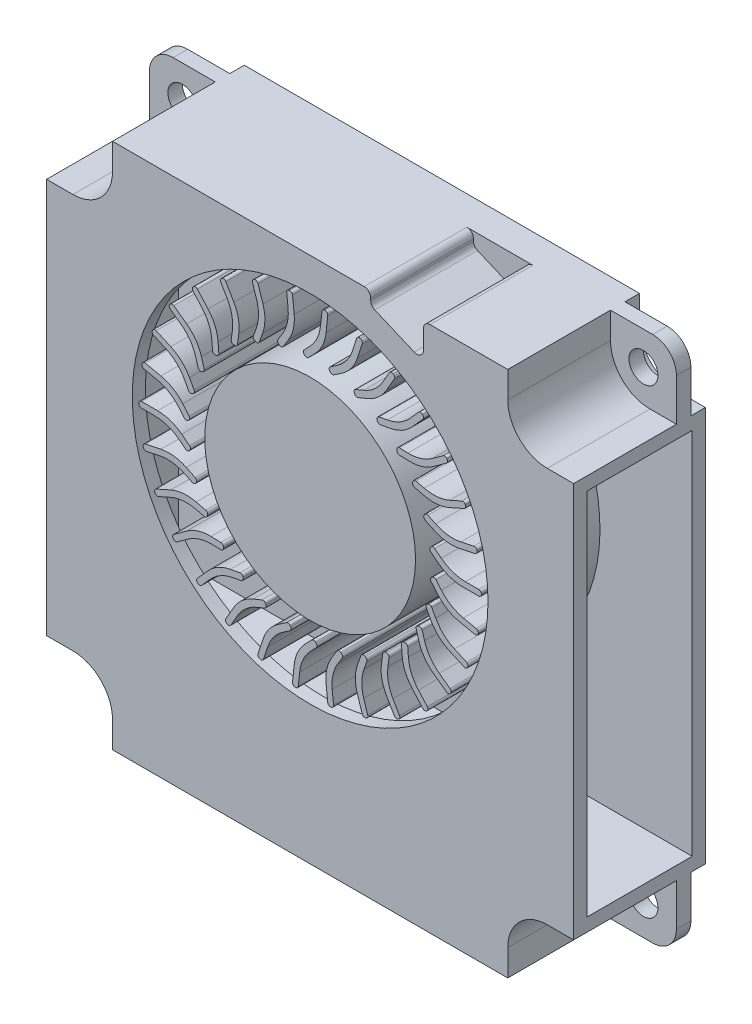
SolidWorks part; units mm, degrees
ref_plane "前视基准面" through (0, 0, 0) normal (0, 0, 1) x (1, 0, 0)
ref_plane "上视基准面" through (0, 0, 0) normal (0, 1, 0) x (1, 0, 0)
ref_plane "右视基准面" through (0, 0, 0) normal (1, 0, 0) x (0, 0, -1)
sketch "草图1" plane through (0, 0, 0) normal (0, 0, 1) x (1, 0, 0)
  line L0 (0, 0) -> (19303.9639, 0) construction
  line L1 (0, 0) -> (0, 19303.9639) construction
  line L3 (-18.2, 20) -> (18.2, 20)
  line L4 (-20, 18.2) -> (-20, -18.2)
  line L5 (-18.2, -20) -> (18.2, -20)
  line L6 (20, 18.2) -> (20, -18.2)
  circle A0 centre (17.5, 17.5) radius 1.1
  circle A1 centre (17.5, -17.5) radius 1.1
  circle A2 centre (-17.5, -17.5) radius 1.1
  circle A3 centre (-17.5, 17.5) radius 1.1
  arc A4 (-20, -18.2) -> (-18.2, -20) centre (-18.2, -18.2) ccw
  arc A5 (18.2, -20) -> (20, -18.2) centre (18.2, -18.2) ccw
  arc A6 (18.2, 20) -> (20, 18.2) centre (18.2, 18.2) cw
  arc A7 (-18.2, 20) -> (-20, 18.2) centre (-18.2, 18.2) ccw
  point P20 (0, 0)
  point P22 (20, -20)
  point P25 (20, 20)
  point P28 (-20, 20)
  point P29 (0, 0)
  point P30 (0, 0)
  point P31 (0, 0)
  point P32 (0, 0)
  point P33 (0, 0)
  point P34 (0, 0)
  point P35 (0, 0)
  point P36 (0, 0)
  point P37 (0, 0)
  point P38 (13.6155, 15.9544)
  point P39 (14.9053, -16.2042)
  point P40 (0, 0)
  point P41 (0, 0)
  point P42 (-13.1755, -15.2334)
  point P43 (-10.9074, 13.5723)
  point P44 (0, 0)
  point P45 (0, 0)
  point P46 (0, 0)
  point P47 (0, 0)
  point P48 (0, 0)
  point P49 (0, 0)
  dimension "D3" = 2.2
  dimension "D4" = 35
  dimension "D5" = 35
  dimension "D7" = 1.8
  dimension "D1" = 40
  dimension "D2" = 40
extrude "凸台-拉伸1" add sketch "草图1" along normal blind 1.1
sketch "草图2" plane through (0, 0, 1.1) normal (0, 0, 1) x (1, 0, 0)
  line L0 (0, 0) -> (50000, 0) construction
  line L1 (0, 0) -> (0, 50000) construction
  line L2 (-20, 15) -> (-18, 15)
  line L3 (-15, 20) -> (4.1, 20)
  line L4 (-20, 15) -> (-20, -15)
  line L5 (-15, -20) -> (15, -20)
  line L6 (20, 15) -> (20, -15)
  line L7 (-15, 18) -> (-15, 20)
  line L8 (18, 15) -> (20, 15)
  line L9 (15, 20) -> (15, 18)
  line L10 (15, -18) -> (15, -20)
  line L11 (20, -15) -> (18, -15)
  line L12 (-18, -15) -> (-20, -15)
  line L13 (-15, -20) -> (-15, -18)
  line L14 (8.6, 19.5) -> (8.6, 18.0558)
  line L15 (7.9044, 17.5956) -> (4.9044, 18.8706)
  line L16 (4.6, 19.3308) -> (4.6, 19.5)
  line L17 (9.1, 20) -> (15, 20)
  arc A0 (-18, -15) -> (-15, -18) centre (-18, -18) cw
  arc A1 (15, -18) -> (18, -15) centre (18, -18) cw
  arc A2 (18, 15) -> (15, 18) centre (18, 18) cw
  arc A3 (-18, 15) -> (-15, 18) centre (-18, 18) ccw
  arc A4 (4.9044, 18.8706) -> (4.6, 19.3308) centre (5.1, 19.3308) cw
  arc A5 (4.6, 19.5) -> (4.1, 20) centre (4.1, 19.5) ccw
  arc A6 (8.6, 19.5) -> (9.1, 20) centre (9.1, 19.5) cw
  arc A7 (8.6, 18.0558) -> (7.9044, 17.5956) centre (8.1, 18.0558) cw
  point P24 (0, 0)
  point P26 (-15, 15)
  point P33 (4.6, 19)
  point P36 (4.6, 20)
  point P39 (8.6, 20)
  point P42 (8.6, 17.3)
  dimension "D1" = 3
  dimension "D13" = 0.5
  dimension "D2" = 40
  dimension "D3" = 5
  dimension "D4" = 5
  dimension "D6" = 40
  dimension "D7" = 5
  dimension "D8" = 5
  dimension "D9" = 6.4
  dimension "D10" = 2.7
  dimension "D11" = 4
  dimension "D12" = 1
  dimension "D5" = 4
extrude "凸台-拉伸2" add sketch "草图2" along normal blind 7.8
sketch "草图3" plane through (0, 0, 0) normal (0, 0, -1) x (-1, 0, 0)
  line L0 (0, 0) -> (50000, 0) construction
  line L1 (-15, 20) -> (15, 20)
  line L2 (-20, 15) -> (-20, -15)
  line L3 (-15, -20) -> (15, -20)
  line L4 (20, 15) -> (20, -15)
  line L5 (0, 0) -> (0, 50000) construction
  line L6 (-20, 15) -> (-18, 15)
  line L7 (-15, 18) -> (-15, 20)
  line L8 (18, 15) -> (20, 15)
  line L9 (15, 20) -> (15, 18)
  line L10 (15, -18) -> (15, -20)
  line L11 (20, -15) -> (18, -15)
  line L12 (-18, -15) -> (-20, -15)
  line L13 (-15, -20) -> (-15, -18)
  line L14 (-18.2, 20) -> (18.2, 20) construction
  arc A0 (-18, -15) -> (-15, -18) centre (-18, -18) cw
  arc A1 (15, -18) -> (18, -15) centre (18, -18) cw
  arc A2 (18, 15) -> (15, 18) centre (18, 18) cw
  arc A3 (-18, 15) -> (-15, 18) centre (-18, 18) ccw
  point P24 (0, 0)
  point P26 (-15, 15)
  dimension "D1" = 3
  dimension "D2" = 40
  dimension "D3" = 5
  dimension "D4" = 5
  dimension "D6" = 40
  dimension "D7" = 5
  dimension "D8" = 5
  dimension "D5" = 4
extrude "凸台-拉伸3" add sketch "草图3" along normal blind 1.1
sketch "草图4" plane through (20, 0, 0) normal (1, 0, 0) x (0, 0, -1)
  line L0 (1.1, 15) -> (1.1, -15) construction
  line L1 (-7.9, 14) -> (0.1, 14)
  line L2 (-7.9, 14) -> (-7.9, -14)
  line L3 (-7.9, -14) -> (0.1, -14)
  line L4 (0.1, 14) -> (0.1, -14)
  line L5 (-8.9, -15) -> (-8.9, 15) construction
  line L6 (-8.9, 15) -> (-1.1, 15) construction
  line L7 (-8.9, -15) -> (-1.1, -15) construction
  point P8 (-5, 15)
  dimension "D1" = 1
  dimension "D2" = 1
  dimension "D3" = 1
  dimension "D4" = 1
extrude "切除-拉伸1" cut sketch "草图4" against normal blind 39
sketch "草图5" plane through (0, 0, 8.9) normal (0, 0, 1) x (1, 0, 0)
  line L0 (4.1, 20) -> (-15, 20) construction
  circle A0 centre (0, 4) radius 13.5
  dimension "D2" = 27
  dimension "D1" = 16
extrude "切除-拉伸2" cut sketch "草图5" against normal blind 9
sketch "草图6" plane through (0, 0, -0.1) normal (0, 0, 1) x (1, 0, 0)
  circle A0 centre (0, 4) radius 13
  dimension "D1" = 26
extrude "凸台-拉伸4" add sketch "草图6" along normal blind 1
sketch "草图7" plane through (0, 0, 0.9) normal (0, 0, 1) x (1, 0, 0)
  line L0 (0, 4) -> (50000, 4) construction
  line L1 (0.3943, 4.0838) -> (48907.7743, 10399.6683) construction
  line L2 (12.7966, 4) -> (11.5807, 4)
  line L3 (9.7456, 4.6267) -> (9.1582, 5.0809)
  line L4 (9.1223, 5.3615) -> (9.1713, 5.4248)
  line L5 (9.4519, 5.4607) -> (9.9575, 5.0697)
  line L6 (11.7926, 4.443) -> (12.7958, 4.443)
  line L7 (12.9958, 4.2464) -> (12.9965, 4.2034)
  line L8 (12.5169, 1.3394) -> (11.3276, 1.5922)
  line L9 (9.6629, 2.5868) -> (9.1828, 3.1532)
  line L10 (9.2061, 3.4351) -> (9.2671, 3.4869)
  line L11 (9.549, 3.4636) -> (9.9623, 2.9761)
  line L12 (11.627, 1.9815) -> (12.6083, 1.7729)
  line L13 (12.763, 1.539) -> (12.7548, 1.4968)
  line L14 (11.6902, -1.2048) -> (10.5795, -0.7103)
  line L15 (9.158, 0.6087) -> (8.8061, 1.2625)
  line L16 (8.8874, 1.5334) -> (8.9579, 1.5713)
  line L17 (9.2288, 1.49) -> (9.5317, 0.9272)
  line L18 (10.9532, -0.3918) -> (11.8698, -0.7998)
  line L19 (11.9725, -1.0608) -> (11.9557, -1.1003)
  line L20 (10.3526, -3.5216) -> (9.369, -2.807)
  line L21 (8.2527, -1.2213) -> (8.0445, -0.5086)
  line L22 (8.1804, -0.2605) -> (8.2572, -0.2381)
  line L23 (8.5053, -0.3739) -> (8.6845, -0.9874)
  line L24 (9.8008, -2.5731) -> (10.6124, -3.1628)
  line L25 (10.6587, -3.4394) -> (10.634, -3.4746)
  line L26 (8.5626, -5.5097) -> (7.749, -4.6061)
  line L27 (6.9868, -2.823) -> (6.9313, -2.0826)
  line L28 (7.1158, -1.8682) -> (7.1956, -1.8622)
  line L29 (7.41, -2.0467) -> (7.4578, -2.684)
  line L30 (8.22, -4.4672) -> (8.8913, -5.2127)
  line L31 (8.879, -5.4929) -> (8.8475, -5.5222)
  line L32 (6.3983, -7.0821) -> (5.7904, -6.0292)
  line L33 (5.4156, -4.1266) -> (5.5152, -3.3908)
  line L34 (5.7403, -3.2194) -> (5.8196, -3.2302)
  line L35 (5.9909, -3.4552) -> (5.9052, -4.0885)
  line L36 (6.2799, -5.9912) -> (6.7816, -6.86)
  line L37 (6.7113, -7.1315) -> (6.6744, -7.1536)
  line L38 (3.9544, -8.1703) -> (3.5786, -7.0139)
  line L39 (3.6076, -5.0749) -> (3.8581, -4.376)
  line L40 (4.1138, -4.2551) -> (4.1892, -4.2821)
  line L41 (4.31, -4.5379) -> (4.0944, -5.1395)
  line L42 (4.0654, -7.0785) -> (4.3754, -8.0327)
  line L43 (4.2503, -8.2836) -> (4.2096, -8.2976)
  line L44 (1.3376, -8.7265) -> (1.2105, -7.5173)
  line L45 (1.642, -5.6267) -> (2.0323, -4.9951)
  line L46 (2.3076, -4.9301) -> (2.3757, -4.9721)
  line L47 (2.4407, -5.2474) -> (2.1047, -5.7911)
  line L48 (1.6732, -7.6817) -> (1.7781, -8.6794)
  line L49 (1.6035, -8.8989) -> (1.5608, -8.9041)
  line L50 (-1.3376, -8.7265) -> (-1.2105, -7.5173)
  line L51 (-0.3954, -5.7577) -> (0.1177, -5.221)
  line L52 (0.4005, -5.2147) -> (0.4583, -5.27)
  line L53 (0.4647, -5.5528) -> (0.023, -6.0147)
  line L54 (-0.7921, -7.7743) -> (-0.897, -8.772)
  line L55 (-1.1134, -8.9504) -> (-1.1562, -8.9466)
  line L56 (-3.9544, -8.1703) -> (-3.5786, -7.0139)
  line L57 (-2.4155, -5.4623) -> (-1.802, -5.044)
  line L58 (-1.5241, -5.0966) -> (-1.479, -5.1627)
  line L59 (-1.5316, -5.4406) -> (-2.0596, -5.8007)
  line L60 (-3.2228, -7.3523) -> (-3.5328, -8.3065)
  line L61 (-3.7816, -8.4359) -> (-3.8227, -8.4233)
  line L62 (-6.3983, -7.0821) -> (-5.7904, -6.0292)
  line L63 (-4.33, -4.7533) -> (-3.643, -4.4717)
  line L64 (-3.3821, -4.5809) -> (-3.3517, -4.655)
  line L65 (-3.4609, -4.9159) -> (-4.0523, -5.1583)
  line L66 (-5.5126, -6.4342) -> (-6.0143, -7.303)
  line L67 (-6.2845, -7.3779) -> (-6.3221, -7.357)
  line L68 (-8.5626, -5.5097) -> (-7.749, -4.6061)
  line L69 (-6.0553, -3.6618) -> (-5.3248, -3.5292)
  line L70 (-5.0923, -3.6902) -> (-5.078, -3.769)
  line L71 (-5.239, -4.0015) -> (-5.8679, -4.1156)
  line L72 (-7.5616, -5.06) -> (-8.2329, -5.8056)
  line L73 (-8.5128, -5.8226) -> (-8.5452, -5.7944)
  line L74 (-10.3526, -3.5216) -> (-9.369, -2.807)
  line L75 (-7.516, -2.2354) -> (-6.7738, -2.2576)
  line L76 (-6.5799, -2.4634) -> (-6.5823, -2.5435)
  line L77 (-6.7881, -2.7374) -> (-7.427, -2.7183)
  line L78 (-9.28, -3.2899) -> (-10.0917, -3.8796)
  line L79 (-10.369, -3.8381) -> (-10.3949, -3.8037)
  line L80 (-11.6902, -1.2048) -> (-10.5795, -0.7103)
  line L81 (-8.6481, -0.5365) -> (-7.9268, -0.7125)
  line L82 (-7.7799, -0.9542) -> (-7.7989, -1.0319)
  line L83 (-8.0406, -1.1788) -> (-8.6615, -1.0273)
  line L84 (-10.5929, -1.2012) -> (-11.5094, -1.6092)
  line L85 (-11.772, -1.511) -> (-11.7902, -1.472)
  line L86 (-12.5169, 1.3394) -> (-11.3276, 1.5922)
  line L87 (-9.4023, 1.3607) -> (-8.7333, 1.0386)
  line L88 (-8.6399, 0.7716) -> (-8.6747, 0.6995)
  line L89 (-8.9416, 0.6061) -> (-9.5175, 0.8834)
  line L90 (-11.4428, 1.1149) -> (-12.4241, 0.9063)
  line L91 (-12.6606, 1.057) -> (-12.6702, 1.0989)
  line L92 (-12.7966, 4) -> (-11.5807, 4)
  line L93 (-9.7456, 3.3733) -> (-9.1582, 2.9191)
  line L94 (-9.1223, 2.6385) -> (-9.1713, 2.5752)
  line L95 (-9.4519, 2.5393) -> (-9.9575, 2.9303)
  line L96 (-11.7926, 3.557) -> (-12.7958, 3.557)
  line L97 (-12.9958, 3.7536) -> (-12.9965, 3.7966)
  line L98 (-12.5169, 6.6606) -> (-11.3276, 6.4078)
  line L99 (-9.6629, 5.4132) -> (-9.1828, 4.8468)
  line L100 (-9.2061, 4.5649) -> (-9.2671, 4.5131)
  line L101 (-9.549, 4.5364) -> (-9.9623, 5.0239)
  line L102 (-11.627, 6.0185) -> (-12.6083, 6.2271)
  line L103 (-12.763, 6.461) -> (-12.7548, 6.5032)
  line L104 (-11.6902, 9.2048) -> (-10.5795, 8.7103)
  line L105 (-9.158, 7.3913) -> (-8.8061, 6.7375)
  line L106 (-8.8874, 6.4666) -> (-8.9579, 6.4287)
  line L107 (-9.2288, 6.51) -> (-9.5317, 7.0728)
  line L108 (-10.9532, 8.3918) -> (-11.8698, 8.7998)
  line L109 (-11.9725, 9.0608) -> (-11.9557, 9.1003)
  line L110 (-10.3526, 11.5216) -> (-9.369, 10.807)
  line L111 (-8.2527, 9.2213) -> (-8.0445, 8.5086)
  line L112 (-8.1804, 8.2605) -> (-8.2572, 8.2381)
  line L113 (-8.5053, 8.3739) -> (-8.6845, 8.9874)
  line L114 (-9.8008, 10.5731) -> (-10.6124, 11.1628)
  line L115 (-10.6587, 11.4394) -> (-10.634, 11.4746)
  line L116 (-8.5626, 13.5097) -> (-7.749, 12.6061)
  line L117 (-6.9868, 10.823) -> (-6.9313, 10.0826)
  line L118 (-7.1158, 9.8682) -> (-7.1956, 9.8622)
  line L119 (-7.41, 10.0467) -> (-7.4578, 10.684)
  line L120 (-8.22, 12.4672) -> (-8.8913, 13.2127)
  line L121 (-8.879, 13.4929) -> (-8.8475, 13.5222)
  line L122 (-6.3983, 15.0821) -> (-5.7904, 14.0292)
  line L123 (-5.4156, 12.1266) -> (-5.5152, 11.3908)
  line L124 (-5.7403, 11.2194) -> (-5.8196, 11.2302)
  line L125 (-5.9909, 11.4552) -> (-5.9052, 12.0885)
  line L126 (-6.2799, 13.9912) -> (-6.7816, 14.86)
  line L127 (-6.7113, 15.1315) -> (-6.6744, 15.1536)
  line L128 (-3.9544, 16.1703) -> (-3.5786, 15.0139)
  line L129 (-3.6076, 13.0749) -> (-3.8581, 12.376)
  line L130 (-4.1138, 12.2551) -> (-4.1892, 12.2821)
  line L131 (-4.31, 12.5379) -> (-4.0944, 13.1395)
  line L132 (-4.0654, 15.0785) -> (-4.3754, 16.0327)
  line L133 (-4.2503, 16.2836) -> (-4.2096, 16.2976)
  line L134 (-1.3376, 16.7265) -> (-1.2105, 15.5173)
  line L135 (-1.642, 13.6267) -> (-2.0323, 12.9951)
  line L136 (-2.3076, 12.9301) -> (-2.3757, 12.9721)
  line L137 (-2.4407, 13.2474) -> (-2.1047, 13.7911)
  line L138 (-1.6732, 15.6817) -> (-1.7781, 16.6794)
  line L139 (-1.6035, 16.8989) -> (-1.5608, 16.9041)
  line L140 (1.3376, 16.7265) -> (1.2105, 15.5173)
  line L141 (0.3954, 13.7577) -> (-0.1177, 13.221)
  line L142 (-0.4005, 13.2147) -> (-0.4583, 13.27)
  line L143 (-0.4647, 13.5528) -> (-0.023, 14.0147)
  line L144 (0.7921, 15.7743) -> (0.897, 16.772)
  line L145 (1.1134, 16.9504) -> (1.1562, 16.9466)
  line L146 (3.9544, 16.1703) -> (3.5786, 15.0139)
  line L147 (2.4155, 13.4623) -> (1.802, 13.044)
  line L148 (1.5241, 13.0966) -> (1.479, 13.1627)
  line L149 (1.5316, 13.4406) -> (2.0596, 13.8007)
  line L150 (3.2228, 15.3523) -> (3.5328, 16.3065)
  line L151 (3.7816, 16.4359) -> (3.8227, 16.4233)
  line L152 (6.3983, 15.0821) -> (5.7904, 14.0292)
  line L153 (4.33, 12.7533) -> (3.643, 12.4717)
  line L154 (3.3821, 12.5809) -> (3.3517, 12.655)
  line L155 (3.4609, 12.9159) -> (4.0523, 13.1583)
  line L156 (5.5126, 14.4342) -> (6.0143, 15.303)
  line L157 (6.2845, 15.3779) -> (6.3221, 15.357)
  line L158 (8.5626, 13.5097) -> (7.749, 12.6061)
  line L159 (6.0553, 11.6618) -> (5.3248, 11.5292)
  line L160 (5.0923, 11.6902) -> (5.078, 11.769)
  line L161 (5.239, 12.0015) -> (5.8679, 12.1156)
  line L162 (7.5616, 13.06) -> (8.2329, 13.8056)
  line L163 (8.5128, 13.8226) -> (8.5452, 13.7944)
  line L164 (10.3526, 11.5216) -> (9.369, 10.807)
  line L165 (7.516, 10.2354) -> (6.7738, 10.2576)
  line L166 (6.5799, 10.4634) -> (6.5823, 10.5435)
  line L167 (6.7881, 10.7374) -> (7.427, 10.7183)
  line L168 (9.28, 11.2899) -> (10.0917, 11.8796)
  line L169 (10.369, 11.8381) -> (10.3949, 11.8037)
  line L170 (11.6902, 9.2048) -> (10.5795, 8.7103)
  line L171 (8.6481, 8.5365) -> (7.9268, 8.7125)
  line L172 (7.7799, 8.9542) -> (7.7989, 9.0319)
  line L173 (8.0406, 9.1788) -> (8.6615, 9.0273)
  line L174 (10.5929, 9.2012) -> (11.5094, 9.6092)
  line L175 (11.772, 9.511) -> (11.7902, 9.472)
  line L176 (12.5169, 6.6606) -> (11.3276, 6.4078)
  line L177 (9.4023, 6.6393) -> (8.7333, 6.9614)
  line L178 (8.6399, 7.2284) -> (8.6747, 7.3005)
  line L179 (8.9416, 7.3939) -> (9.5175, 7.1166)
  line L180 (11.4428, 6.8851) -> (12.4241, 7.0937)
  line L181 (12.6606, 6.943) -> (12.6702, 6.9011)
  circle A0 centre (0, 4) radius 8
  circle A1 centre (0, 4) radius 13 construction
  arc A2 (11.5807, 4) -> (9.7456, 4.6267) centre (11.5807, 7) cw
  arc A3 (9.9575, 5.0697) -> (11.7926, 4.443) centre (11.7926, 7.443) ccw
  arc A4 (12.7966, 4) -> (12.9965, 4.2034) centre (12.7966, 4.2) ccw
  arc A5 (12.7958, 4.443) -> (12.9958, 4.2464) centre (12.7958, 4.243) cw
  arc A6 (9.1582, 5.0809) -> (9.1223, 5.3615) centre (9.2806, 5.2392) cw
  arc A7 (9.1713, 5.4248) -> (9.4519, 5.4607) centre (9.3295, 5.3025) cw
  arc A8 (11.3276, 1.5922) -> (9.6629, 2.5868) centre (11.9514, 4.5267) cw
  arc A9 (9.9623, 2.9761) -> (11.627, 1.9815) centre (12.2507, 4.9159) ccw
  arc A10 (12.5169, 1.3394) -> (12.7548, 1.4968) centre (12.5585, 1.5351) ccw
  arc A11 (12.6083, 1.7729) -> (12.763, 1.539) centre (12.5667, 1.5773) cw
  arc A12 (9.1828, 3.1532) -> (9.2061, 3.4351) centre (9.3354, 3.2825) cw
  arc A13 (9.2671, 3.4869) -> (9.549, 3.4636) centre (9.3965, 3.3343) cw
  arc A14 (10.5795, -0.7103) -> (9.158, 0.6087) centre (11.7997, 2.0303) cw
  arc A15 (9.5317, 0.9272) -> (10.9532, -0.3918) centre (12.1735, 2.3489) ccw
  arc A16 (11.6902, -1.2048) -> (11.9557, -1.1003) centre (11.7716, -1.0221) ccw
  arc A17 (11.8698, -0.7998) -> (11.9725, -1.0608) centre (11.7884, -0.9825) cw
  arc A18 (8.8061, 1.2625) -> (8.8874, 1.5334) centre (8.9822, 1.3573) cw
  arc A19 (8.9579, 1.5713) -> (9.2288, 1.49) centre (9.0527, 1.3952) cw
  arc A20 (9.369, -2.807) -> (8.2527, -1.2213) centre (11.1324, -0.3799) cw
  arc A21 (8.6845, -0.9874) -> (9.8008, -2.5731) centre (11.5641, -0.1461) ccw
  arc A22 (10.3526, -3.5216) -> (10.634, -3.4746) centre (10.4702, -3.3598) ccw
  arc A23 (10.6124, -3.1628) -> (10.6587, -3.4394) centre (10.4949, -3.3246) cw
  arc A24 (8.0445, -0.5086) -> (8.1804, -0.2605) centre (8.2365, -0.4525) cw
  arc A25 (8.2572, -0.2381) -> (8.5053, -0.3739) centre (8.3133, -0.43) cw
  arc A26 (7.749, -4.6061) -> (6.9868, -2.823) centre (9.9784, -2.5988) cw
  arc A27 (7.4578, -2.684) -> (8.22, -4.4672) centre (10.4494, -2.4598) ccw
  arc A28 (8.5626, -5.5097) -> (8.8475, -5.5222) centre (8.7112, -5.3759) ccw
  arc A29 (8.8913, -5.2127) -> (8.879, -5.4929) centre (8.7427, -5.3466) cw
  arc A30 (6.9313, -2.0826) -> (7.1158, -1.8682) centre (7.1308, -2.0676) cw
  arc A31 (7.1956, -1.8622) -> (7.41, -2.0467) centre (7.2106, -2.0617) cw
  arc A32 (5.7904, -6.0292) -> (5.4156, -4.1266) centre (8.3884, -4.5292) cw
  arc A33 (5.9052, -4.0885) -> (6.2799, -5.9912) centre (8.878, -4.4912) ccw
  arc A34 (6.3983, -7.0821) -> (6.6744, -7.1536) centre (6.5715, -6.9821) ccw
  arc A35 (6.7816, -6.86) -> (6.7113, -7.1315) centre (6.6084, -6.96) cw
  arc A36 (5.5152, -3.3908) -> (5.7403, -3.2194) centre (5.7134, -3.4176) cw
  arc A37 (5.8196, -3.2302) -> (5.9909, -3.4552) centre (5.7927, -3.4284) cw
  arc A38 (3.5786, -7.0139) -> (3.6076, -5.0749) centre (6.4318, -6.0869) cw
  arc A39 (4.0944, -5.1395) -> (4.0654, -7.0785) centre (6.9186, -6.1515) ccw
  arc A40 (3.9544, -8.1703) -> (4.2096, -8.2976) centre (4.1446, -8.1085) ccw
  arc A41 (4.3754, -8.0327) -> (4.2503, -8.2836) centre (4.1852, -8.0945) cw
  arc A42 (3.8581, -4.376) -> (4.1138, -4.2551) centre (4.0464, -4.4434) cw
  arc A43 (4.1892, -4.2821) -> (4.31, -4.5379) centre (4.1217, -4.4704) cw
  arc A44 (1.2105, -7.5173) -> (1.642, -5.6267) centre (4.1941, -7.2037) cw
  arc A45 (2.1047, -5.7911) -> (1.6732, -7.6817) centre (4.6568, -7.3681) ccw
  arc A46 (1.3376, -8.7265) -> (1.5608, -8.9041) centre (1.5365, -8.7056) ccw
  arc A47 (1.7781, -8.6794) -> (1.6035, -8.8989) centre (1.5792, -8.7003) cw
  arc A48 (2.0323, -4.9951) -> (2.3076, -4.9301) centre (2.2024, -5.1002) cw
  arc A49 (2.3757, -4.9721) -> (2.4407, -5.2474) centre (2.2705, -5.1423) cw
  arc A50 (-1.2105, -7.5173) -> (-0.3954, -5.7577) centre (1.7731, -7.8309) cw
  arc A51 (0.023, -6.0147) -> (-0.7921, -7.7743) centre (2.1915, -8.0879) ccw
  arc A52 (-1.3376, -8.7265) -> (-1.1562, -8.9466) centre (-1.1387, -8.7474) ccw
  arc A53 (-0.897, -8.772) -> (-1.1134, -8.9504) centre (-1.0959, -8.7511) cw
  arc A54 (0.1177, -5.221) -> (0.4005, -5.2147) centre (0.2623, -5.3592) cw
  arc A55 (0.4583, -5.27) -> (0.4647, -5.5528) centre (0.3201, -5.4146) cw
  arc A56 (-3.5786, -7.0139) -> (-2.4155, -5.4623) centre (-0.7255, -7.941) cw
  arc A57 (-2.0596, -5.8007) -> (-3.2228, -7.3523) centre (-0.3696, -8.2794) ccw
  arc A58 (-3.9544, -8.1703) -> (-3.8227, -8.4233) centre (-3.7641, -8.2321) ccw
  arc A59 (-3.5328, -8.3065) -> (-3.7816, -8.4359) centre (-3.723, -8.2446) cw
  arc A60 (-1.802, -5.044) -> (-1.5241, -5.0966) centre (-1.6893, -5.2093) cw
  arc A61 (-1.479, -5.1627) -> (-1.5316, -5.4406) centre (-1.6443, -5.2754) cw
  arc A62 (-5.7904, -6.0292) -> (-4.33, -4.7533) centre (-3.1923, -7.5292) cw
  arc A63 (-4.0523, -5.1583) -> (-5.5126, -6.4342) centre (-2.9146, -7.9342) ccw
  arc A64 (-6.3983, -7.0821) -> (-6.3221, -7.357) centre (-6.2251, -7.1821) ccw
  arc A65 (-6.0143, -7.303) -> (-6.2845, -7.3779) centre (-6.1875, -7.203) cw
  arc A66 (-3.643, -4.4717) -> (-3.3821, -4.5809) centre (-3.5671, -4.6568) cw
  arc A67 (-3.3517, -4.655) -> (-3.4609, -4.9159) centre (-3.5368, -4.7308) cw
  arc A68 (-7.749, -4.6061) -> (-6.0553, -3.6618) centre (-5.5196, -6.6135) cw
  arc A69 (-5.8679, -4.1156) -> (-7.5616, -5.06) centre (-5.3321, -7.0674) ccw
  arc A70 (-8.5626, -5.5097) -> (-8.5452, -5.7944) centre (-8.4139, -5.6435) ccw
  arc A71 (-8.2329, -5.8056) -> (-8.5128, -5.8226) centre (-8.3815, -5.6718) cw
  arc A72 (-5.3248, -3.5292) -> (-5.0923, -3.6902) centre (-5.289, -3.726) cw
  arc A73 (-5.078, -3.769) -> (-5.239, -4.0015) centre (-5.2747, -3.8047) cw
  arc A74 (-9.369, -2.807) -> (-7.516, -2.2354) centre (-7.6056, -5.234) cw
  arc A75 (-7.427, -2.7183) -> (-9.28, -3.2899) centre (-7.5167, -5.7169) ccw
  arc A76 (-10.3526, -3.5216) -> (-10.3949, -3.8037) centre (-10.2351, -3.6834) ccw
  arc A77 (-10.0917, -3.8796) -> (-10.369, -3.8381) centre (-10.2092, -3.7178) cw
  arc A78 (-6.7738, -2.2576) -> (-6.5799, -2.4634) centre (-6.7798, -2.4575) cw
  arc A79 (-6.5823, -2.5435) -> (-6.7881, -2.7374) centre (-6.7822, -2.5375) cw
  arc A80 (-10.5795, -0.7103) -> (-8.6481, -0.5365) centre (-9.3593, -3.4509) cw
  arc A81 (-8.6615, -1.0273) -> (-10.5929, -1.2012) centre (-9.3727, -3.9418) ccw
  arc A82 (-11.6902, -1.2048) -> (-11.7902, -1.472) centre (-11.6089, -1.3875) ccw
  arc A83 (-11.5094, -1.6092) -> (-11.772, -1.511) centre (-11.5907, -1.4265) cw
  arc A84 (-7.9268, -0.7125) -> (-7.7799, -0.9542) centre (-7.9742, -0.9068) cw
  arc A85 (-7.7989, -1.0319) -> (-8.0406, -1.1788) centre (-7.9932, -0.9845) cw
  arc A86 (-11.3276, 1.5922) -> (-9.4023, 1.3607) centre (-10.7039, -1.3422) cw
  arc A87 (-9.5175, 0.8834) -> (-11.4428, 1.1149) centre (-10.819, -1.8196) ccw
  arc A88 (-12.5169, 1.3394) -> (-12.6702, 1.0989) centre (-12.4753, 1.1438) ccw
  arc A89 (-12.4241, 0.9063) -> (-12.6606, 1.057) centre (-12.4657, 1.1019) cw
  arc A90 (-8.7333, 1.0386) -> (-8.6399, 0.7716) centre (-8.8201, 0.8584) cw
  arc A91 (-8.6747, 0.6995) -> (-8.9416, 0.6061) centre (-8.8549, 0.7863) cw
  arc A92 (-11.5807, 4) -> (-9.7456, 3.3733) centre (-11.5807, 1) cw
  arc A93 (-9.9575, 2.9303) -> (-11.7926, 3.557) centre (-11.7926, 0.557) ccw
  arc A94 (-12.7966, 4) -> (-12.9965, 3.7966) centre (-12.7966, 3.8) ccw
  arc A95 (-12.7958, 3.557) -> (-12.9958, 3.7536) centre (-12.7958, 3.757) cw
  arc A96 (-9.1582, 2.9191) -> (-9.1223, 2.6385) centre (-9.2806, 2.7608) cw
  arc A97 (-9.1713, 2.5752) -> (-9.4519, 2.5393) centre (-9.3295, 2.6975) cw
  arc A98 (-11.3276, 6.4078) -> (-9.6629, 5.4132) centre (-11.9514, 3.4733) cw
  arc A99 (-9.9623, 5.0239) -> (-11.627, 6.0185) centre (-12.2507, 3.0841) ccw
  arc A100 (-12.5169, 6.6606) -> (-12.7548, 6.5032) centre (-12.5585, 6.4649) ccw
  arc A101 (-12.6083, 6.2271) -> (-12.763, 6.461) centre (-12.5667, 6.4227) cw
  arc A102 (-9.1828, 4.8468) -> (-9.2061, 4.5649) centre (-9.3354, 4.7175) cw
  arc A103 (-9.2671, 4.5131) -> (-9.549, 4.5364) centre (-9.3965, 4.6657) cw
  arc A104 (-10.5795, 8.7103) -> (-9.158, 7.3913) centre (-11.7997, 5.9697) cw
  arc A105 (-9.5317, 7.0728) -> (-10.9532, 8.3918) centre (-12.1735, 5.6511) ccw
  arc A106 (-11.6902, 9.2048) -> (-11.9557, 9.1003) centre (-11.7716, 9.0221) ccw
  arc A107 (-11.8698, 8.7998) -> (-11.9725, 9.0608) centre (-11.7884, 8.9825) cw
  arc A108 (-8.8061, 6.7375) -> (-8.8874, 6.4666) centre (-8.9822, 6.6427) cw
  arc A109 (-8.9579, 6.4287) -> (-9.2288, 6.51) centre (-9.0527, 6.6048) cw
  arc A110 (-9.369, 10.807) -> (-8.2527, 9.2213) centre (-11.1324, 8.3799) cw
  arc A111 (-8.6845, 8.9874) -> (-9.8008, 10.5731) centre (-11.5641, 8.1461) ccw
  arc A112 (-10.3526, 11.5216) -> (-10.634, 11.4746) centre (-10.4702, 11.3598) ccw
  arc A113 (-10.6124, 11.1628) -> (-10.6587, 11.4394) centre (-10.4949, 11.3246) cw
  arc A114 (-8.0445, 8.5086) -> (-8.1804, 8.2605) centre (-8.2365, 8.4525) cw
  arc A115 (-8.2572, 8.2381) -> (-8.5053, 8.3739) centre (-8.3133, 8.43) cw
  arc A116 (-7.749, 12.6061) -> (-6.9868, 10.823) centre (-9.9784, 10.5988) cw
  arc A117 (-7.4578, 10.684) -> (-8.22, 12.4672) centre (-10.4494, 10.4598) ccw
  arc A118 (-8.5626, 13.5097) -> (-8.8475, 13.5222) centre (-8.7112, 13.3759) ccw
  arc A119 (-8.8913, 13.2127) -> (-8.879, 13.4929) centre (-8.7427, 13.3466) cw
  arc A120 (-6.9313, 10.0826) -> (-7.1158, 9.8682) centre (-7.1308, 10.0676) cw
  arc A121 (-7.1956, 9.8622) -> (-7.41, 10.0467) centre (-7.2106, 10.0617) cw
  arc A122 (-5.7904, 14.0292) -> (-5.4156, 12.1266) centre (-8.3884, 12.5292) cw
  arc A123 (-5.9052, 12.0885) -> (-6.2799, 13.9912) centre (-8.878, 12.4912) ccw
  arc A124 (-6.3983, 15.0821) -> (-6.6744, 15.1536) centre (-6.5715, 14.9821) ccw
  arc A125 (-6.7816, 14.86) -> (-6.7113, 15.1315) centre (-6.6084, 14.96) cw
  arc A126 (-5.5152, 11.3908) -> (-5.7403, 11.2194) centre (-5.7134, 11.4176) cw
  arc A127 (-5.8196, 11.2302) -> (-5.9909, 11.4552) centre (-5.7927, 11.4284) cw
  arc A128 (-3.5786, 15.0139) -> (-3.6076, 13.0749) centre (-6.4318, 14.0869) cw
  arc A129 (-4.0944, 13.1395) -> (-4.0654, 15.0785) centre (-6.9186, 14.1515) ccw
  arc A130 (-3.9544, 16.1703) -> (-4.2096, 16.2976) centre (-4.1446, 16.1085) ccw
  arc A131 (-4.3754, 16.0327) -> (-4.2503, 16.2836) centre (-4.1852, 16.0945) cw
  arc A132 (-3.8581, 12.376) -> (-4.1138, 12.2551) centre (-4.0464, 12.4434) cw
  arc A133 (-4.1892, 12.2821) -> (-4.31, 12.5379) centre (-4.1217, 12.4704) cw
  arc A134 (-1.2105, 15.5173) -> (-1.642, 13.6267) centre (-4.1941, 15.2037) cw
  arc A135 (-2.1047, 13.7911) -> (-1.6732, 15.6817) centre (-4.6568, 15.3681) ccw
  arc A136 (-1.3376, 16.7265) -> (-1.5608, 16.9041) centre (-1.5365, 16.7056) ccw
  arc A137 (-1.7781, 16.6794) -> (-1.6035, 16.8989) centre (-1.5792, 16.7003) cw
  arc A138 (-2.0323, 12.9951) -> (-2.3076, 12.9301) centre (-2.2024, 13.1002) cw
  arc A139 (-2.3757, 12.9721) -> (-2.4407, 13.2474) centre (-2.2705, 13.1423) cw
  arc A140 (1.2105, 15.5173) -> (0.3954, 13.7577) centre (-1.7731, 15.8309) cw
  arc A141 (-0.023, 14.0147) -> (0.7921, 15.7743) centre (-2.1915, 16.0879) ccw
  arc A142 (1.3376, 16.7265) -> (1.1562, 16.9466) centre (1.1387, 16.7474) ccw
  arc A143 (0.897, 16.772) -> (1.1134, 16.9504) centre (1.0959, 16.7511) cw
  arc A144 (-0.1177, 13.221) -> (-0.4005, 13.2147) centre (-0.2623, 13.3592) cw
  arc A145 (-0.4583, 13.27) -> (-0.4647, 13.5528) centre (-0.3201, 13.4146) cw
  arc A146 (3.5786, 15.0139) -> (2.4155, 13.4623) centre (0.7255, 15.941) cw
  arc A147 (2.0596, 13.8007) -> (3.2228, 15.3523) centre (0.3696, 16.2794) ccw
  arc A148 (3.9544, 16.1703) -> (3.8227, 16.4233) centre (3.7641, 16.2321) ccw
  arc A149 (3.5328, 16.3065) -> (3.7816, 16.4359) centre (3.723, 16.2446) cw
  arc A150 (1.802, 13.044) -> (1.5241, 13.0966) centre (1.6893, 13.2093) cw
  arc A151 (1.479, 13.1627) -> (1.5316, 13.4406) centre (1.6443, 13.2754) cw
  arc A152 (5.7904, 14.0292) -> (4.33, 12.7533) centre (3.1923, 15.5292) cw
  arc A153 (4.0523, 13.1583) -> (5.5126, 14.4342) centre (2.9146, 15.9342) ccw
  arc A154 (6.3983, 15.0821) -> (6.3221, 15.357) centre (6.2251, 15.1821) ccw
  arc A155 (6.0143, 15.303) -> (6.2845, 15.3779) centre (6.1875, 15.203) cw
  arc A156 (3.643, 12.4717) -> (3.3821, 12.5809) centre (3.5671, 12.6568) cw
  arc A157 (3.3517, 12.655) -> (3.4609, 12.9159) centre (3.5368, 12.7308) cw
  arc A158 (7.749, 12.6061) -> (6.0553, 11.6618) centre (5.5196, 14.6135) cw
  arc A159 (5.8679, 12.1156) -> (7.5616, 13.06) centre (5.3321, 15.0674) ccw
  arc A160 (8.5626, 13.5097) -> (8.5452, 13.7944) centre (8.4139, 13.6435) ccw
  arc A161 (8.2329, 13.8056) -> (8.5128, 13.8226) centre (8.3815, 13.6718) cw
  arc A162 (5.3248, 11.5292) -> (5.0923, 11.6902) centre (5.289, 11.726) cw
  arc A163 (5.078, 11.769) -> (5.239, 12.0015) centre (5.2747, 11.8047) cw
  arc A164 (9.369, 10.807) -> (7.516, 10.2354) centre (7.6056, 13.234) cw
  arc A165 (7.427, 10.7183) -> (9.28, 11.2899) centre (7.5167, 13.7169) ccw
  arc A166 (10.3526, 11.5216) -> (10.3949, 11.8037) centre (10.2351, 11.6834) ccw
  arc A167 (10.0917, 11.8796) -> (10.369, 11.8381) centre (10.2092, 11.7178) cw
  arc A168 (6.7738, 10.2576) -> (6.5799, 10.4634) centre (6.7798, 10.4575) cw
  arc A169 (6.5823, 10.5435) -> (6.7881, 10.7374) centre (6.7822, 10.5375) cw
  arc A170 (10.5795, 8.7103) -> (8.6481, 8.5365) centre (9.3593, 11.4509) cw
  arc A171 (8.6615, 9.0273) -> (10.5929, 9.2012) centre (9.3727, 11.9418) ccw
  arc A172 (11.6902, 9.2048) -> (11.7902, 9.472) centre (11.6089, 9.3875) ccw
  arc A173 (11.5094, 9.6092) -> (11.772, 9.511) centre (11.5907, 9.4265) cw
  arc A174 (7.9268, 8.7125) -> (7.7799, 8.9542) centre (7.9742, 8.9068) cw
  arc A175 (7.7989, 9.0319) -> (8.0406, 9.1788) centre (7.9932, 8.9845) cw
  arc A176 (11.3276, 6.4078) -> (9.4023, 6.6393) centre (10.7039, 9.3422) cw
  arc A177 (9.5175, 7.1166) -> (11.4428, 6.8851) centre (10.819, 9.8196) ccw
  arc A178 (12.5169, 6.6606) -> (12.6702, 6.9011) centre (12.4753, 6.8562) ccw
  arc A179 (12.4241, 7.0937) -> (12.6606, 6.943) centre (12.4657, 6.8981) cw
  arc A180 (8.7333, 6.9614) -> (8.6399, 7.2284) centre (8.8201, 7.1416) cw
  arc A181 (8.6747, 7.3005) -> (8.9416, 7.3939) centre (8.8549, 7.2137) cw
  point P17 (10.5561, 4)
  point P22 (13, 4)
  point P25 (12.9924, 4.443)
  point P28 (9, 5.2033)
  point P556 (0, 4)
  dimension "D1" = 16
  dimension "D4" = 3
  dimension "D5" = 0.2
  dimension "D2" = 12
  dimension "D3" = 4
  dimension "D6" = 30
extrude "凸台-拉伸5" add sketch "草图7" along normal blind 8
